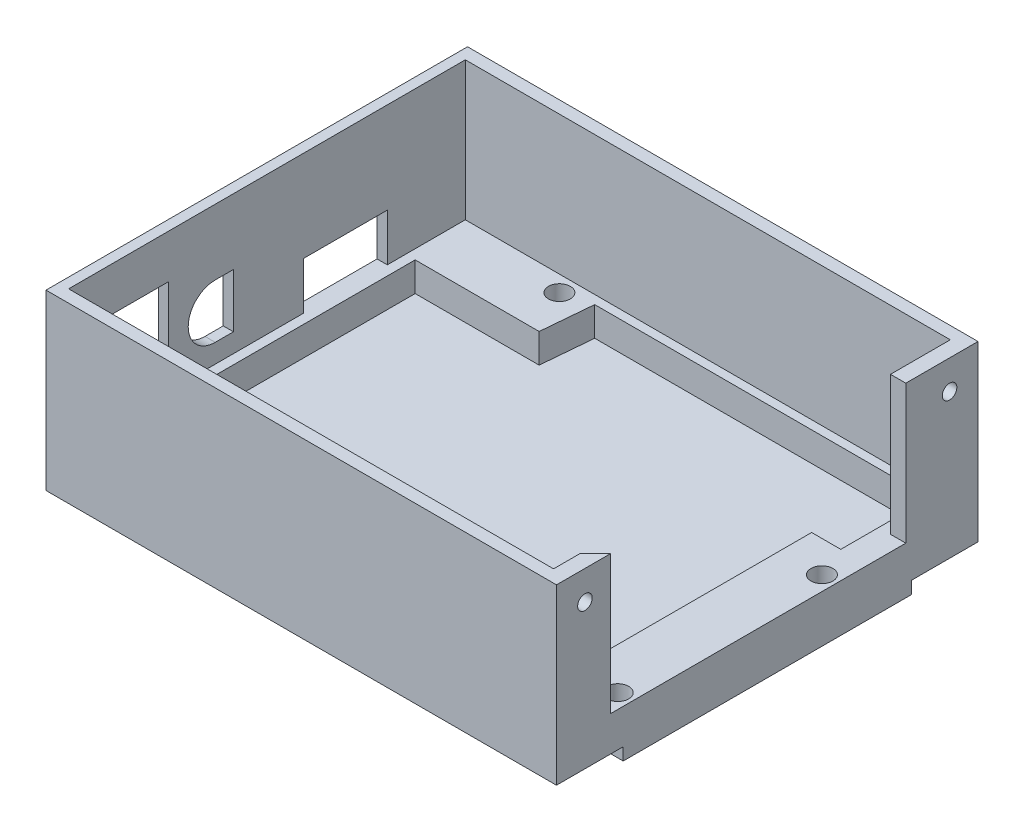
SolidWorks part; units mm, degrees
ref_plane "前视基准面" through (0, 0, 0) normal (0, 0, 1) x (1, 0, 0)
ref_plane "上视基准面" through (0, 0, 0) normal (0, 1, 0) x (1, 0, 0)
ref_plane "右视基准面" through (0, 0, 0) normal (1, 0, 0) x (0, 0, -1)
other "Configuration Table"
sketch "草图1" plane through (0, 0, 0) normal (0, 1, 0) x (1, 0, 0)
  line L1 (33, -27) -> (-33, -27)
  line L2 (33, -27) -> (33, -24)
  line L3 (33, 27) -> (-33, 27)
  line L4 (-33, -27) -> (-33, 27)
  line L5 (33, -27) -> (-33, 27) construction
  line L6 (33, 27) -> (-33, -27) construction
  line L7 (36, 11) -> (36, -21)
  line L9 (33, 14) -> (33, 27)
  line L10 (36, 11) -> (33, 14)
  line L11 (33, -24) -> (36, -21)
  line L12 (-31.7778, 26) -> (-31.7778, -26)
  line L13 (-31.7778, -26) -> (31.7778, -26)
  line L14 (31.7778, -26) -> (31.7778, -23.808)
  line L15 (31.7778, -23.808) -> (35, -20.5858)
  line L16 (35, -20.5858) -> (35, 9.5438)
  line L18 (31.7778, 13.808) -> (31.7778, 26)
  line L19 (31.7778, 26) -> (-31.7778, 26)
  line L20 (31.7778, 13.808) -> (35, 10.5858)
  line L22 (35, 9.5438) -> (35, 10.5858)
  point P0 (0, 0)
  dimension "D1" = 66
  dimension "D2" = 54
  dimension "D3" = 6
  dimension "D4" = 3
  dimension "D5" = 3
  dimension "D6" = 13
  dimension "D7" = 16
  dimension "D8" = 52
  dimension "D9" = 1
  dimension "D10" = 1
  dimension "D11" = 1
extrude "凸台-拉伸1" add sketch "草图1" against normal blind 4
sketch "草图3" plane through (0, 0, 0) normal (0, 1, 0) x (1, 0, 0)
  line L1 (-35, 29) -> (38, 29)
  line L2 (-35, 29) -> (-35, -29)
  line L3 (-35, -29) -> (38, -29)
  line L4 (38, 29) -> (38, -29)
  line L5 (33, 27) -> (33, 14)
  line L6 (-33, 27) -> (33, 27)
  line L7 (-33, 27) -> (-33, -27)
  line L8 (-33, -27) -> (33, -27)
  line L9 (36, 11) -> (36, -21)
  line L10 (33, 14) -> (36, 11)
  line L11 (33, -27) -> (33, -24)
  line L12 (33, -24) -> (36, -21)
  dimension "D1" = 2
  dimension "D2" = 2
  dimension "D3" = 2
  dimension "D4" = 2
extrude "凸台-拉伸2" add sketch "草图3" against normal blind 4 and the other way blind 13
sketch "草图4" plane through (0, 0, 0) normal (0, 1, 0) x (1, 0, 0)
  line L0 (-31.7778, 26) -> (-14.7778, 26)
  line L1 (31.7778, 26) -> (-31.7778, 26) construction
  line L2 (-14.7778, 26) -> (-14.7778, 19)
  line L3 (-14.7778, 19) -> (-31.7778, 19)
  line L4 (-31.7778, 26) -> (-31.7778, -26) construction
  line L5 (-31.7778, 19) -> (-31.7778, 26)
  line L6 (31.7778, 13.808) -> (27.7778, 13.808)
  line L7 (27.7778, 13.808) -> (27.7778, -22)
  line L8 (27.7778, -22) -> (33.5858, -22)
  line L9 (31.7778, -23.808) -> (35, -20.5858) construction
  line L10 (-31.7778, -26) -> (31.7778, -26) construction
  line L11 (31.7778, 13.808) -> (35, 10.5858)
  line L12 (35, 10.5858) -> (35, -20.5858)
  line L13 (35, -20.5858) -> (33.5858, -22)
  dimension "D1" = 17
  dimension "D2" = 7
  dimension "D3" = 4
  dimension "D4" = 4
extrude "凸台-拉伸4" add sketch "草图4" against normal blind 4
sketch "草图5" plane through (0, 0, 0) normal (0, 1, 0) x (1, 0, 0)
  line L0 (-33, 27) -> (-33, -27) construction
  line L3 (33, 27) -> (-33, 27) construction
  line L4 (36, -21) -> (36, 11) construction
  line L6 (27.7778, 13.808) -> (27.7778, -22) construction
  circle A0 centre (-18, 25) radius 1.5
  circle A1 centre (33.5, 9.5) radius 1.5
  circle A2 centre (33.5, -18.5) radius 1.5
  dimension "D3" = 3
  dimension "D6" = 3
  dimension "D8" = 3
  dimension "D1" = 15
  dimension "D2" = 2
  dimension "D4" = 17.5
  dimension "D5" = 2.5
  dimension "D7" = 28
  dimension "D9" = 5.7222
extrude "切除-拉伸1" cut sketch "草图5" against normal blind 4
sketch "草图6" plane through (0, -4, 0) normal (0, -1, 0) x (1, 0, 0)
  line L0 (31.7778, 23.808) -> (33.5858, 22)
  line L1 (33.5858, 22) -> (30.6818, 22)
  line L2 (27.7778, 22) -> (33.5858, 22) construction
  line L3 (30.6818, 22) -> (31.7778, 23.808)
extrude "凸台-拉伸5" add sketch "草图6" against normal blind 4
sketch "草图7" plane through (0, 0, 0) normal (0, 1, 0) x (1, 0, 0)
  line L0 (-14.159, 26) -> (-14.7778, 19)
  line L1 (31.7778, 26) -> (-14.7778, 26) construction
  line L2 (-14.7778, 19) -> (-14.7778, 26)
  line L3 (-14.7778, 26) -> (-14.159, 26)
extrude "凸台-拉伸6" add sketch "草图7" against normal blind 4
sketch "草图8" plane through (0, -4, 0) normal (0, -1, 0) x (1, 0, 0)
  line L1 (-35, 29) -> (38, 29)
  line L2 (-35, 29) -> (-35, -29)
  line L3 (-35, -29) -> (38, -29)
  line L4 (38, 29) -> (38, -29)
extrude "凸台-拉伸7" add sketch "草图8" along normal blind 1
sketch "草图9" plane through (-33, 0, 0) normal (1, 0, 0) x (0, 0, -1)
  line L0 (6, 4.5) -> (6, 1)
  line L1 (6, 1) -> (14.5, 1)
  line L2 (14.5, 1) -> (14.5, 4.5)
  line L3 (14.5, 4.5) -> (6, 4.5)
  line L4 (27, 13) -> (27, 0) construction
  line L5 (27, 0) -> (-27, 0) construction
  dimension "D1" = 21
  dimension "D2" = 1
  dimension "D3" = 4.5
  dimension "D4" = 8.5
extrude "切除-拉伸2" cut sketch "草图9" against normal blind 2
chamfer "倒角1" distance 0.5 angle 45 4 edges at (-35, 1, -10.25) (-35, 2.75, -14.5) (-35, 2.75, -6) (-35, 4.5, -10.25)
sketch "草图10" plane through (-33, 0, 0) normal (1, 0, 0) x (0, 0, -1)
  line L0 (27, 0) -> (-27, 0) construction
  line L1 (-23, 12) -> (-14, 12)
  line L2 (-23, 12) -> (-23, 0)
  line L3 (-23, 0) -> (-14, 0)
  line L4 (-14, 12) -> (-14, 0)
  line L5 (-27, 13) -> (-27, 0) construction
  dimension "D1" = 13
  dimension "D2" = 12
  dimension "D3" = 9
extrude "切除-拉伸3" cut sketch "草图10" against normal blind 2
chamfer "倒角2" distance 0.5 angle 45 4 edges at (-35, 12, 18.5) (-35, 0, 18.5) (-35, 6, 14) (-35, 6, 23)
chamfer "倒角3" distance 0.5 angle 45 3 edges at (-33, 1, -10.25) (-33, 4.5, -10.25) (-33, 12, 18.5)
chamfer "倒角4" distance 0.5 angle 45 4 edges at (-33, 6.25, 14) (-33, 6.25, 23) (-33, 2.75, -6) (-33, 2.75, -14.5)
sketch "草图13" plane through (-33, 0, 0) normal (1, 0, 0) x (0, 0, -1)
  line L0 (-27, 13) -> (-27, 0) construction
  line L1 (-6, 8.6) -> (-7.1, 8.6)
  line L2 (-6, 8.6) -> (-6, 4)
  line L3 (-6, 4) -> (-7.1, 4)
  line L4 (27, 0) -> (-13.5, 0) construction
  arc A1 (-7.1, 8.6) -> (-7.1, 4) centre (-7.1, 6.3) ccw
  dimension "D1" = 21
  dimension "D2" = 1.1
  dimension "D3" = 4.6
  dimension "D4" = 1.1
  dimension "D5" = 4
extrude "切除-拉伸4" cut sketch "草图13" against normal blind 2
sketch "草图15" plane through (-33, 0, 0) normal (1, 0, 0) x (0, 0, -1)
chamfer "倒角5" distance 0.5 angle 45 4 edges at (-35, 4, 6.55) (-35, 6.3, 6) (-35, 8.6, 6.55) (-35, 6.3, 9.4)
chamfer "倒角6" distance 0.5 angle 45 4 edges at (-33, 4, 6.55) (-33, 6.3, 6) (-33, 8.6, 6.55) (-33, 6.3, 9.4)
sketch "草图21" plane through (0, 13, 0) normal (0, 1, 0) x (1, 0, 0)
  line L0 (-35, -29) -> (38, -29) construction
  line L1 (38, 29) -> (36, 29)
  line L2 (38, 29) -> (38, -29)
  line L3 (38, -29) -> (36, -29)
  line L4 (36, 29) -> (36, -29)
  dimension "D1" = 2
extrude "切除-拉伸5" cut sketch "草图21" against normal through all
sketch "草图23" plane through (0, 13, 0) normal (0, 1, 0) x (1, 0, 0)
  line L0 (33, 14) -> (33, 19)
  line L1 (33, 14) -> (33, 27) construction
  line L2 (33, 19) -> (36, 19)
  line L3 (36, 29) -> (36, 11) construction
  line L4 (36, 19) -> (36, 11)
  line L5 (36, 11) -> (33, 14)
  dimension "D1" = 5
extrude "切除-拉伸7" cut sketch "草图23" against normal up to surface (13 mm away) up to face at (-18, 0, -23.5)
sketch "草图27" plane through (0, 13, 0) normal (0, 1, 0) x (1, 0, 0)
  line L12 (33, 19) -> (36, 19)
  line L13 (36, 19) -> (36, 29)
  line L14 (36, 29) -> (-35, 29)
  line L15 (-35, 29) -> (-35, -29)
  line L16 (-35, -29) -> (36, -29)
  line L17 (36, -29) -> (36, -21)
  line L18 (36, -21) -> (33, -24)
  line L19 (33, -24) -> (33, -27)
  line L20 (33, -27) -> (-33, -27)
  line L21 (-33, -27) -> (-33, 27)
  line L22 (-33, 27) -> (33, 27)
  line L23 (33, 27) -> (33, 19)
  line L24 (33, 19) -> (36, 19)
  line L25 (36, 19) -> (36, 29)
  line L26 (36, 29) -> (-35, 29)
  line L27 (-35, 29) -> (-35, -29)
  line L28 (-35, -29) -> (36, -29)
  line L29 (36, -29) -> (36, -21)
  line L30 (36, -21) -> (33, -24)
  line L31 (33, -24) -> (33, -27)
  line L32 (33, -27) -> (-33, -27)
  line L33 (-33, -27) -> (-33, 27)
  line L34 (-33, 27) -> (33, 27)
  line L35 (33, 27) -> (33, 19)
  dimension "D1" = 0
extrude "凸台-拉伸8" add sketch "草图27" along normal blind 6
sketch "草图36" plane through (0, -5, 0) normal (0, -1, 0) x (1, 0, 0)
  line L0 (-35, 29) -> (-35, -29) construction
  line L10 (-35, 19.75) -> (36, 19.75)
  line L11 (-35, 19.75) -> (-35, -19.75)
  line L12 (-35, -19.75) -> (36, -19.75)
  line L13 (36, 19.75) -> (36, -19.75)
  line L14 (36, -29) -> (36, 29) construction
  point P8 (-35, 0)
  dimension "D1" = 39.5
extrude "凸台-拉伸9" add sketch "草图36" along normal blind 1.5
sketch "草图39" plane through (36, 0, 0) normal (1, 0, 0) x (0, 0, -1)
  line L0 (-29, -5) -> (-29, 19) construction
  line L1 (29, -5) -> (29, 19) construction
  line L2 (-29, 19) -> (-21, 19) construction
  line L3 (19, 19) -> (29, 19) construction
  circle A0 centre (-25, 15) radius 1
  circle A1 centre (25, 15) radius 1
  dimension "D1" = 2
  dimension "D2" = 2
  dimension "D3" = 4
  dimension "D4" = 4
  dimension "D5" = 4
  dimension "D6" = 4
extrude "切除-拉伸9" cut sketch "草图39" against normal blind 5
sketch "草图42" plane through (36, 0, 0) normal (1, 0, 0) x (0, 0, -1)
  line L0 (29, -5) -> (29, 19) construction
  line L1 (-29, -5) -> (-19.75, -5)
  line L2 (-29, -5) -> (-29, -4.8)
  line L3 (-29, -4.8) -> (-19.75, -4.8)
  line L4 (-19.75, -5) -> (-19.75, -4.8)
  line L5 (19.75, -5) -> (29, -5)
  line L6 (19.75, -5) -> (19.75, -4.8)
  line L7 (19.75, -4.8) -> (29, -4.8)
  line L8 (29, -5) -> (29, -4.8)
  dimension "D1" = 0.2
  dimension "D2" = 0.2
extrude "切除-拉伸10" cut sketch "草图42" against normal through all
sketch "草图43" plane through (36, 0, 0) normal (1, 0, 0) x (0, 0, -1)
  line L1 (-19.75, -4.8) -> (-29, -4.8) construction
  line L2 (-29, 19) -> (-28.9, 19)
  line L3 (-29, 19) -> (-29, -4.8)
  line L4 (-29, -4.8) -> (-28.9, -4.8)
  line L5 (-28.9, 19) -> (-28.9, -4.8)
  line L6 (29, -4.8) -> (19.75, -4.8) construction
  line L7 (29, 19) -> (28.9, 19)
  line L8 (29, 19) -> (29, -4.8)
  line L9 (29, -4.8) -> (28.9, -4.8)
  line L10 (28.9, 19) -> (28.9, -4.8)
  dimension "D1" = 0.1
  dimension "D2" = 0.1
extrude "切除-拉伸11" cut sketch "草图43" against normal through all
sketch "草图44" plane through (36, 0, 0) normal (1, 0, 0) x (0, 0, -1)
  line L24 (19.75, -4.8) -> (28.9, -4.8)
  line L25 (28.9, -4.8) -> (28.9, 19)
  line L26 (28.9, 19) -> (19, 19)
  line L27 (19, 19) -> (19, 0)
  line L28 (19, 0) -> (-21, 0)
  line L29 (-21, 0) -> (-21, 19)
  line L30 (-21, 19) -> (-28.9, 19)
  line L31 (-28.9, 19) -> (-28.9, -4.8)
  line L32 (-28.9, -4.8) -> (-19.75, -4.8)
  line L33 (-19.75, -4.8) -> (-19.75, -6.5)
  line L34 (-19.75, -6.5) -> (19.75, -6.5)
  line L35 (19.75, -6.5) -> (19.75, -4.8)
  line L36 (19.75, -4.8) -> (28.9, -4.8)
  line L37 (28.9, -4.8) -> (28.9, 19)
  line L38 (28.9, 19) -> (19, 19)
  line L39 (19, 19) -> (19, 0)
  line L40 (19, 0) -> (-21, 0)
  line L41 (-21, 0) -> (-21, 19)
  line L42 (-21, 19) -> (-28.9, 19)
  line L43 (-28.9, 19) -> (-28.9, -4.8)
  line L44 (-28.9, -4.8) -> (-19.75, -4.8)
  line L45 (-19.75, -4.8) -> (-19.75, -6.5)
  line L46 (-19.75, -6.5) -> (19.75, -6.5)
  line L47 (19.75, -6.5) -> (19.75, -4.8)
  dimension "D1" = 0
extrude "切除-拉伸12" cut sketch "草图44" against normal blind 0.5
sketch "草图45" plane through (-35, 0, 0) normal (-1, 0, 0) x (0, 0, 1)
  line L8 (28.9, 19) -> (-28.9, 19)
  line L9 (-28.9, 19) -> (-28.9, -4.8)
  line L10 (-28.9, -4.8) -> (-19.75, -4.8)
  line L11 (-19.75, -4.8) -> (-19.75, -6.5)
  line L12 (-19.75, -6.5) -> (19.75, -6.5)
  line L13 (19.75, -6.5) -> (19.75, -4.8)
  line L14 (19.75, -4.8) -> (28.9, -4.8)
  line L15 (28.9, -4.8) -> (28.9, 19)
  line L16 (28.9, 19) -> (-28.9, 19)
  line L17 (-28.9, 19) -> (-28.9, -4.8)
  line L18 (-28.9, -4.8) -> (-19.75, -4.8)
  line L19 (-19.75, -4.8) -> (-19.75, -6.5)
  line L20 (-19.75, -6.5) -> (19.75, -6.5)
  line L21 (19.75, -6.5) -> (19.75, -4.8)
  line L22 (19.75, -4.8) -> (28.9, -4.8)
  line L23 (28.9, -4.8) -> (28.9, 19)
  dimension "D1" = 0
extrude "切除-拉伸13" cut sketch "草图45" against normal blind 0.5
sketch "草图46" plane through (0, 19, 0) normal (0, 1, 0) x (1, 0, 0)
  line L0 (33, 27) -> (-33, 27)
  line L1 (-33, 27) -> (-33, -27)
  line L2 (-33, -27) -> (33, -27)
  line L3 (33, -27) -> (33, 27)
  line L4 (-33.1, 27.2) -> (33.4, 27.2)
  line L5 (33.4, 27.2) -> (33.4, -27.2)
  line L6 (33.4, -27.2) -> (-33.1, -27.2)
  line L7 (-33.1, -27.2) -> (-33.1, 27.2)
  dimension "D1" = 0.2
  dimension "D2" = 0.2
  dimension "D3" = 0.4
  dimension "D4" = 0.1
extrude "切除-拉伸14" cut sketch "草图46" against normal up to surface (19 mm away) up to face at (-4.6429, 0, 8.4643)
sketch "草图47" plane through (-34.5, 0, 0) normal (-1, 0, 0) x (0, 0, 1)
  line L1 (-5, 0) -> (-16.5, 0)
  line L2 (-5, 0) -> (-5, 6.5)
  line L3 (-5, 6.5) -> (-16.5, 6.5)
  line L4 (-16.5, 0) -> (-16.5, 6.5)
  line L5 (-14.5, 4.5) -> (-6, 4.5)
  line L6 (-14.5, 4.5) -> (-14.5, 1)
  line L7 (-14.5, 1) -> (-6, 1)
  line L8 (-6, 4.5) -> (-6, 1)
  dimension "D1" = 2
  dimension "D2" = 1
  dimension "D3" = 2
  dimension "D4" = 1
extrude "切除-拉伸16" cut sketch "草图47" against normal blind 7.5
sketch "草图48" plane through (-33.1, 0, 0) normal (1, 0, 0) x (0, 0, -1)
  line L7 (-7.1, 10) -> (-5.6, 10)
  line L9 (-5.6, 2.6) -> (-7.1, 2.6)
  line L10 (-5.6, 10) -> (-4.6, 10)
  line L11 (-4.6, 10) -> (-4.6, 2.6)
  line L12 (-4.6, 2.6) -> (-5.6, 2.6)
  arc A2 (-7.1, 10) -> (-7.1, 2.6) centre (-7.1, 6.3) ccw
extrude "切除-拉伸17" cut sketch "草图48" against normal blind 7.5
sketch "草图51" plane through (-34.5, 0, 0) normal (-1, 0, 0) x (0, 0, 1)
  line L0 (23.6, 0) -> (21.5, 0) construction
  line L1 (14, 12) -> (21.5, 12)
  line L2 (14, 12) -> (14, 0)
  line L3 (14, 0) -> (21.5, 0)
  line L4 (21.5, 12) -> (21.5, 0)
  line L5 (21.5, 0) -> (21.5, 19) construction
  line L7 (13.5, 13) -> (23.5, 13)
  line L8 (13.5, 13) -> (13.5, -1.5)
  line L9 (13.5, -1.5) -> (23.5, -1.5)
  line L10 (23.5, 13) -> (23.5, -1.5)
  dimension "D1" = 1
  dimension "D2" = 1.5
  dimension "D3" = 2
  dimension "D4" = 0.5
extrude "切除-拉伸18" cut sketch "草图51" against normal blind 7.5
